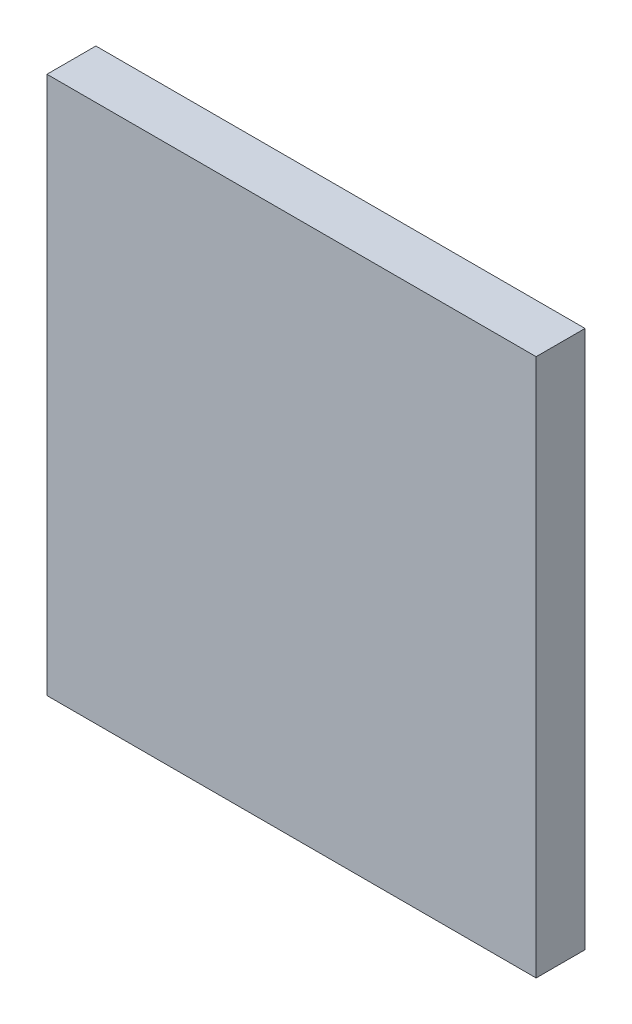
SolidWorks part; units mm, degrees
ref_plane "前视基准面" through (0, 0, 0) normal (0, 0, 1) x (1, 0, 0)
ref_plane "上视基准面" through (0, 0, 0) normal (0, 1, 0) x (1, 0, 0)
ref_plane "右视基准面" through (0, 0, 0) normal (1, 0, 0) x (0, 0, -1)
sketch "草图1" plane through (0, 0, 0) normal (0, 0, 1) x (1, 0, 0)
  line L1 (0, 16.5) -> (-30, 16.5)
  line L2 (0, 16.5) -> (0, -16.5)
  line L3 (0, -16.5) -> (-30, -16.5)
  line L4 (-30, 16.5) -> (-30, -16.5)
  dimension "D1" = 30
extrude "凸台-拉伸1" add sketch "草图1" along normal blind 3
